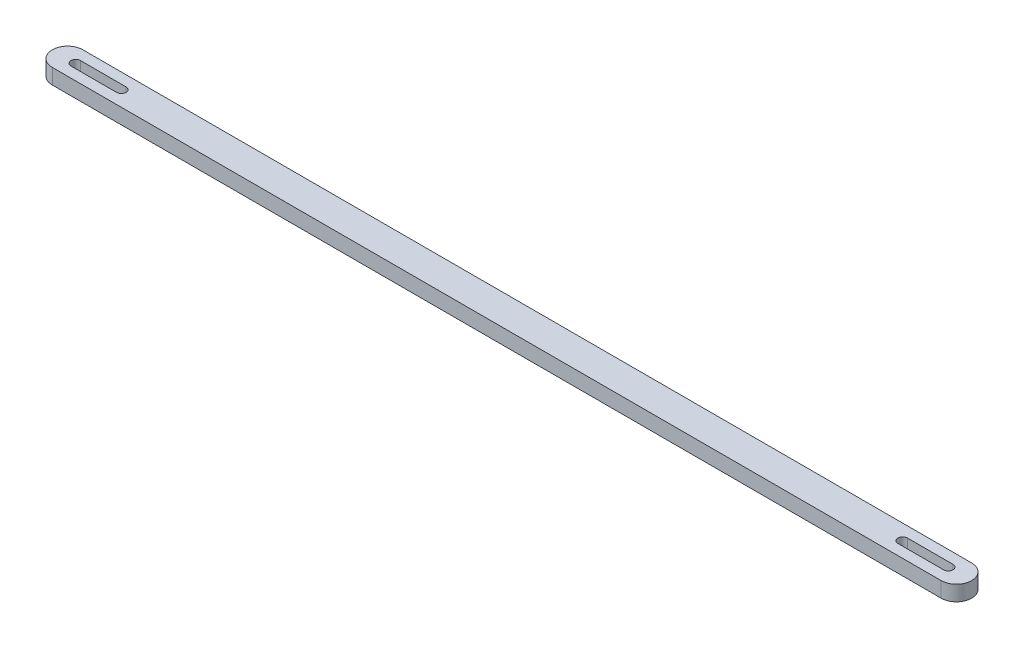
SolidWorks part; units mm, degrees
ref_plane "前基準面" through (0, 0, 0) normal (0, 0, 1) x (1, 0, 0)
ref_plane "上基準面" through (0, 0, 0) normal (0, 1, 0) x (1, 0, 0)
ref_plane "右基準面" through (0, 0, 0) normal (1, 0, 0) x (0, 0, -1)
sketch "草圖1" plane through (0, 0, 0) normal (0, 1, 0) x (1, 0, 0)
  line L0 (-145.5, 0) -> (145.5, 0) construction
  line L1 (-145.5, 5) -> (145.5, 5)
  line L2 (-145.5, -5) -> (145.5, -5)
  line L3 (0, 34.0994) -> (0, -34.0994) construction
  line L4 (-127.8901, 0) -> (-142.8303, 0) construction
  line L5 (-127.8901, -1.55) -> (-142.8303, -1.55)
  line L6 (-127.8901, 1.55) -> (-142.8303, 1.55)
  line L7 (127.8901, 0) -> (142.8303, 0) construction
  line L8 (127.8901, -1.55) -> (142.8303, -1.55)
  line L9 (127.8901, 1.55) -> (142.8303, 1.55)
  arc A0 (-145.5, 5) -> (-145.5, -5) centre (-145.5, 0) ccw
  arc A1 (145.5, -5) -> (145.5, 5) centre (145.5, 0) ccw
  arc A2 (-127.8901, -1.55) -> (-127.8901, 1.55) centre (-127.8901, 0) ccw
  arc A3 (-142.8303, 1.55) -> (-142.8303, -1.55) centre (-142.8303, 0) ccw
  arc A4 (127.8901, -1.55) -> (127.8901, 1.55) centre (127.8901, 0) cw
  arc A5 (142.8303, 1.55) -> (142.8303, -1.55) centre (142.8303, 0) cw
  point P2 (0, 0)
  point P11 (0, 0)
  point P13 (-135.3602, 0)
  point P20 (135.3602, 0)
  dimension "D1" = 10
  dimension "D2" = 291
  dimension "D3" = 3.1
extrude "填料-伸長1" add sketch "草圖1" along normal blind 5
